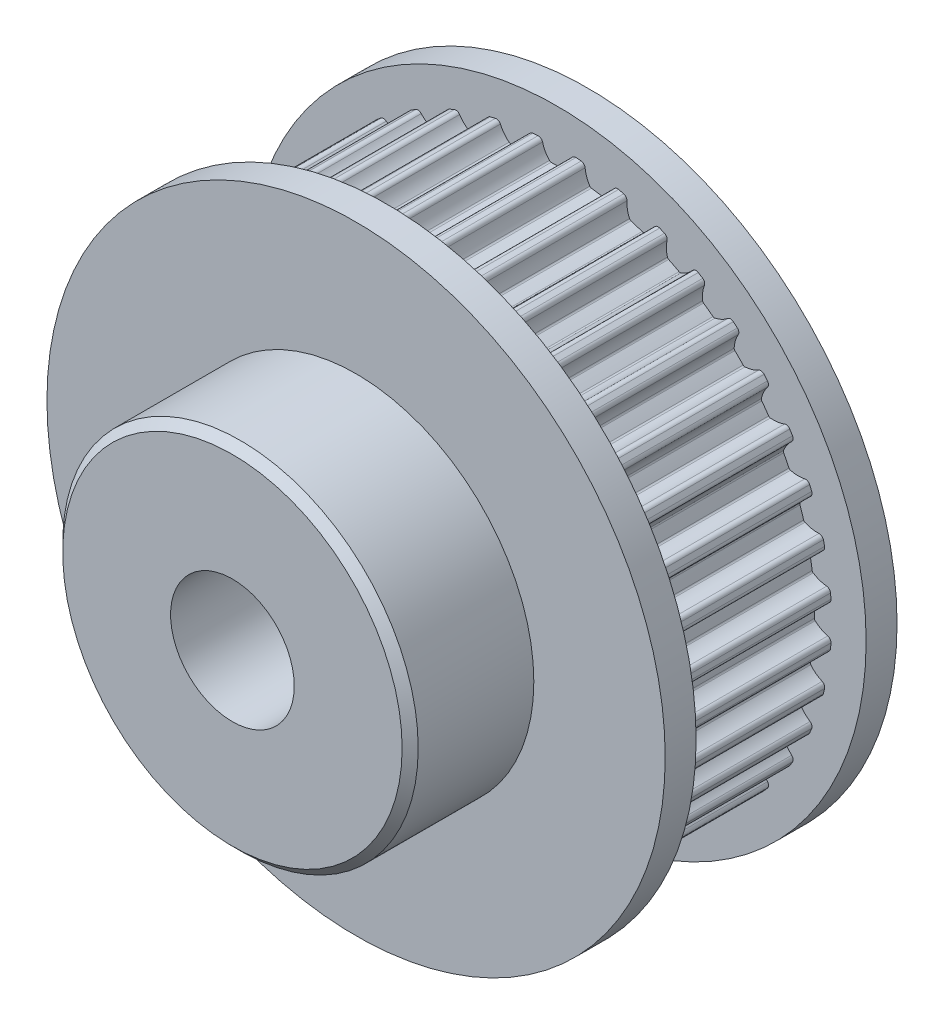
SolidWorks part; units mm, degrees
material "6061-T6 (SS)"
ref_plane "前基準面" through (0, 0, 0) normal (0, 0, 1) x (1, 0, 0)
ref_plane "上基準面" through (0, 0, 0) normal (0, 1, 0) x (1, 0, 0)
ref_plane "右基準面" through (0, 0, 0) normal (1, 0, 0) x (0, 0, -1)
sketch "草圖1" plane through (0, 0, 0) normal (0, 0, 1) x (1, 0, 0)
  circle A0 centre (0, 0) radius 17.765
  dimension "D1" = 35.53
extrude "填料-伸長1" add sketch "草圖1" along normal mid plane 11
sketch "草圖2" plane through (0, 0, 5.5) normal (0, 0, 1) x (1, 0, 0)
  line L0 (0, 0) -> (0, 17.765) construction
  line L1 (0, 17.765) -> (0, 18.019) construction
  line L2 (-0.975, 18.019) -> (0.975, 18.019) construction
  circle A0 centre (0, 0) radius 17.765 construction
  arc A1 (-0.3803, 16.6507) -> (0.3803, 16.6507) centre (0, 0) cw
  arc A2 (-0.3803, 16.6507) -> (-0.4954, 16.7005) centre (-0.3837, 16.8006) cw
  arc A3 (-0.4954, 16.7005) -> (-0.9346, 17.5149) centre (0.975, 18.019) cw
  arc A4 (-1.2246, 17.7227) -> (-0.9346, 17.5149) centre (-1.2053, 17.4434) cw
  arc A5 (0.3803, 16.6507) -> (0.4954, 16.7005) centre (0.3837, 16.8006) ccw
  arc A6 (0.4954, 16.7005) -> (0.9346, 17.5149) centre (-0.975, 18.019) ccw
  arc A7 (1.2246, 17.7227) -> (0.9346, 17.5149) centre (1.2053, 17.4434) ccw
  arc A8 (-1.2246, 17.7227) -> (1.2246, 17.7227) centre (0, 0) cw
  dimension "D1" = 0.15
  dimension "D2" = 1.975
  dimension "D3" = 0.28
  dimension "D4" = 1.11
  dimension "D5" = 0.254
  dimension "D6" = 1.95
extrude "除料-伸長1" cut sketch "草圖2" against normal through all and the other way through all
pattern_circular "環狀複製排列1" count 40 over 360 about axis through (0, 0, 0) along (0, 0, 1) of "除料-伸長1"
sketch "草圖3" plane through (0, 0, 5.5) normal (0, 0, 1) x (1, 0, 0)
  circle A0 centre (0, 0) radius 20
  dimension "D1" = 40
extrude "填料-伸長2" add sketch "草圖3" along normal blind 2
sketch "草圖9" plane through (0, 0, -5.5) normal (0, 0, -1) x (-1, 0, 0)
  circle A0 centre (0, 0) radius 20
  circle A1 centre (0, 0) radius 20 construction
extrude "填料-伸長3" add sketch "草圖9" along normal blind 2
sketch "Sketch1" plane through (0, 0, 7.5) normal (0, 0, 1) x (1, 0, 0)
  circle A0 centre (0, 0) radius 11.5
  dimension "D1" = 23
extrude "Boss-Extrude1" add sketch "Sketch1" along normal blind 8 contours A0
sketch "草圖4" plane through (0, 0, 7.5) normal (0, 0, 1) x (1, 0, 0)
  circle A0 centre (0, 0) radius 4
  dimension "D1" = 8
extrude "除料-伸長2" cut sketch "草圖4" against normal through all and the other way through all
chamfer "Chamfer1" distance 0.52 angle 45 1 edges at (11.5, 0, 15.5)
